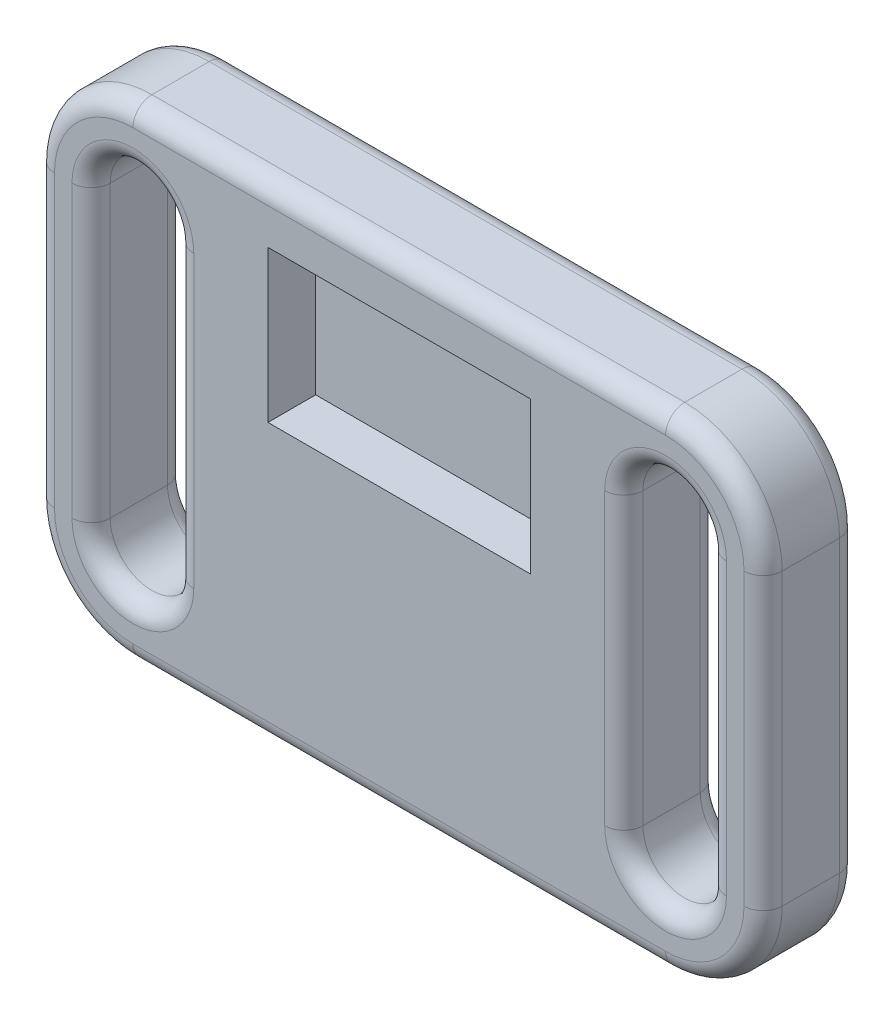
SolidWorks part; units mm, degrees
ref_plane "Front Plane" through (0, 0, 0) normal (0, 0, 1) x (1, 0, 0)
ref_plane "Top Plane" through (0, 0, 0) normal (0, 1, 0) x (1, 0, 0)
ref_plane "Right Plane" through (0, 0, 0) normal (1, 0, 0) x (0, 0, -1)
sketch "Sketch1" plane through (0, 0, 0) normal (0, 0, 1) x (1, 0, 0)
  line L0 (-152.4, -60.7667) -> (-152.4, 60.7667)
  line L1 (-152.4, -101.6) -> (152.4, -101.6) construction
  line L2 (-152.4, -101.6) -> (-152.4, 101.6) construction
  line L3 (-152.4, 101.6) -> (152.4, 101.6) construction
  line L4 (152.4, -101.6) -> (152.4, 101.6) construction
  line L5 (-152.4, -101.6) -> (152.4, 101.6) construction
  line L6 (-152.4, 101.6) -> (152.4, -101.6) construction
  line L7 (-111.5667, 101.6) -> (111.5667, 101.6)
  line L8 (0, 101.6) -> (0, -101.6) construction
  line L9 (152.4, 0) -> (-152.4, 0) construction
  line L10 (-152.4, -101.6) -> (152.4, 101.6) construction
  line L11 (-152.4, -101.6) -> (152.4, -101.6) construction
  line L12 (-111.5667, -101.6) -> (111.5667, -101.6)
  line L13 (152.4, -101.6) -> (-152.4, 101.6) construction
  line L14 (152.4, 101.6) -> (-152.4, -101.6) construction
  line L15 (152.4, -101.6) -> (-152.4, 101.6) construction
  line L16 (152.4, -101.6) -> (152.4, 101.6) construction
  line L17 (152.4, -60.7667) -> (152.4, 60.7667)
  line L18 (-129.0667, 60.7667) -> (-152.4, 60.7667) construction
  line L19 (-129.0667, 60.7667) -> (-94.0667, 60.7667) construction
  line L20 (-129.0667, 60.7667) -> (-129.0667, -60.7667)
  line L21 (-129.0667, -60.7667) -> (-94.0667, -60.7667) construction
  line L22 (-94.0667, 60.7667) -> (-94.0667, -60.7667)
  line L23 (129.0667, 60.7667) -> (129.0667, -60.7667)
  line L24 (94.0667, 60.7667) -> (94.0667, -60.7667)
  arc A0 (-152.4, 60.7667) -> (-111.5667, 101.6) centre (-111.5667, 60.7667) cw
  arc A1 (-152.4, -60.7667) -> (-111.5667, -101.6) centre (-111.5667, -60.7667) ccw
  arc A2 (152.4, -60.7667) -> (111.5667, -101.6) centre (111.5667, -60.7667) cw
  arc A3 (152.4, 60.7667) -> (111.5667, 101.6) centre (111.5667, 60.7667) ccw
  arc A4 (-129.0667, 60.7667) -> (-94.0667, 60.7667) centre (-111.5667, 60.7667) cw
  arc A5 (-129.0667, -60.7667) -> (-94.0667, -60.7667) centre (-111.5667, -60.7667) ccw
  arc A6 (129.0667, -60.7667) -> (94.0667, -60.7667) centre (111.5667, -60.7667) cw
  arc A7 (129.0667, 60.7667) -> (94.0667, 60.7667) centre (111.5667, 60.7667) ccw
  point P0 (0, 0)
  point P17 (0, 0)
  dimension "D1" = 203.2
  dimension "D2" = 304.8
  dimension "D3" = 35
  dimension "D4" = 23.3333
extrude "Steering Wheel Body" add sketch "Sketch1" along normal mid plane 40
fillet "Fillet1" radius 8 32 edges at (111.5667, 78.2667, -20) (129.0667, 0, -20) (111.5667, -78.2667, -20) (94.0667, 0, -20) (-111.5667, -78.2667, -20) (-129.0667, 0, -20) (-111.5667, 78.2667, -20) (-94.0667, 0, -20) (-152.4, 0, -20) (-140.4402, -89.6402, -20) (0, -101.6, -20) (140.4402, -89.6402, -20) (152.4, 0, -20) (140.4402, 89.6402, -20) (0, 101.6, -20) (-140.4402, 89.6402, -20) (129.0667, 0, 20) (111.5667, 78.2667, 20) (94.0667, 0, 20) (111.5667, -78.2667, 20) (0, 101.6, 20) (140.4402, 89.6402, 20) (152.4, 0, 20) (140.4402, -89.6402, 20) (0, -101.6, 20) (-140.4402, -89.6402, 20) (-152.4, 0, 20) (-140.4402, 89.6402, 20) (-129.0667, 0, 20) (-111.5667, -78.2667, 20) (-94.0667, 0, 20) (-111.5667, 78.2667, 20)
sketch "Sketch3" plane through (0, 0, 0) normal (0, 0, 1) x (1, 0, 0)
  line L0 (0, 0) -> (0, 101.6) construction
  line L1 (-54.9926, 15) -> (54.9926, 15)
  line L2 (-54.9926, 15) -> (-54.9926, 78.5)
  line L3 (-54.9926, 78.5) -> (54.9926, 78.5)
  line L4 (54.9926, 15) -> (54.9926, 78.5)
  line L5 (111.5667, 101.6) -> (-111.5667, 101.6) construction
  line L6 (0, 0) -> (152.4, 0) construction
  line L7 (152.4, -60.7667) -> (152.4, 60.7667) construction
  line L8 (-94.0667, -60.7667) -> (-94.0667, 60.7667) construction
  line L9 (-54.9926, 15) -> (54.9926, 78.5) construction
  point P9 (0, 15)
  dimension "D3" = 15
  dimension "D1" = 127
  dimension "D2" = 30
extrude "LCD Cutout" cut sketch "Sketch3" against normal blind 20 from surface at 20 starting at face at (111.5667, 0, 20)
sketch "Sketch5" plane through (0, 0, 0) normal (0, 0, 1) x (1, 0, 0)
  line L0 (0, 0) -> (0, 41.9601) construction
  circle A0 centre (0, 0) radius 41.9601 construction
  point P5 (0, 41.9601)
  dimension "D1" = 83.9201
hole_wizard "M5x0.8 Tapped Hole1" positions "Sketch6" profile "Sketch7" tap size "M5x0.8" standard "ANSI Metric"
sketch "Sketch6" plane through (0, 0, -20) normal (0, 0, -1) x (-1, 0, 0)
  point P0 (0, 41.9601)
sketch "Sketch7" plane through (0, 41.9601, -20) normal (1, 0, 0) x (0, 1, 0)
  line L0 (0, 0) -> (0, 9.6618)
  line L1 (0, 9.6618) -> (2.1, 8.4)
  line L2 (2.1, 8.4) -> (2.1, 0)
  line L5 (2.1, 0) -> (0, 0)
  line L10 (0, 9.6618) -> (-2.1, 8.4) construction
  line L11 (0, -6.35) -> (0, 107.95) construction
  dimension "Tap Drill Dia." = 4.2
  dimension "Tap Drill Depth" = 8.4
  dimension "Drill Angle" = 118
sketch "Sketch8" plane through (0, 0, 0) normal (0, 1, 0) x (1, 0, 0)
  line L0 (0, 52.4568) -> (0, -56.5569) construction
pattern_circular "CirPattern1" count 9 over 360 about axis through (0, 0, 0) along (0, 0, 1) of "M5x0.8 Tapped Hole1"
equation "\"Steering Wheel Height\"= 8in"
equation "\"D1@Sketch1\"=\"Steering Wheel Height\""
equation "\"Steering Wheel Width\"= 12in"
equation "\"D2@Sketch1\"=\"Steering Wheel Width\""
equation "\"Steering Wheel Thickness\"= 35mm"
equation "\"Hand Cutout Width\"= 35mm"
equation "\"D3@Sketch1\"=\"Hand Cutout Width\""
equation "\"D4@Sketch1\"=\"Hand Cutout Width\"*(2/3)"
equation "\"LCD Width\"= \"LCD Size\" * cos ( 30deg )"
equation "\"LCD Height\"= \"LCD Size\" * sin ( 30deg )"
equation "\"LCD Thickness\"= 2cm'Exact thickness is unknown at this time for the LCD specced out"
equation "\"D1@LCD Cutout\" = \"LCD Thickness\""
equation "\"LCD Size\"= 5in"
equation "\"D1@Sketch3\"=\"LCD Size\""
equation "\"Quick Release Diameter\"=83.9201"
equation "\"D1@Sketch5\"=\"Quick Release Diameter\""
equation "\"Number of Holes on Quick Release\"=9"
